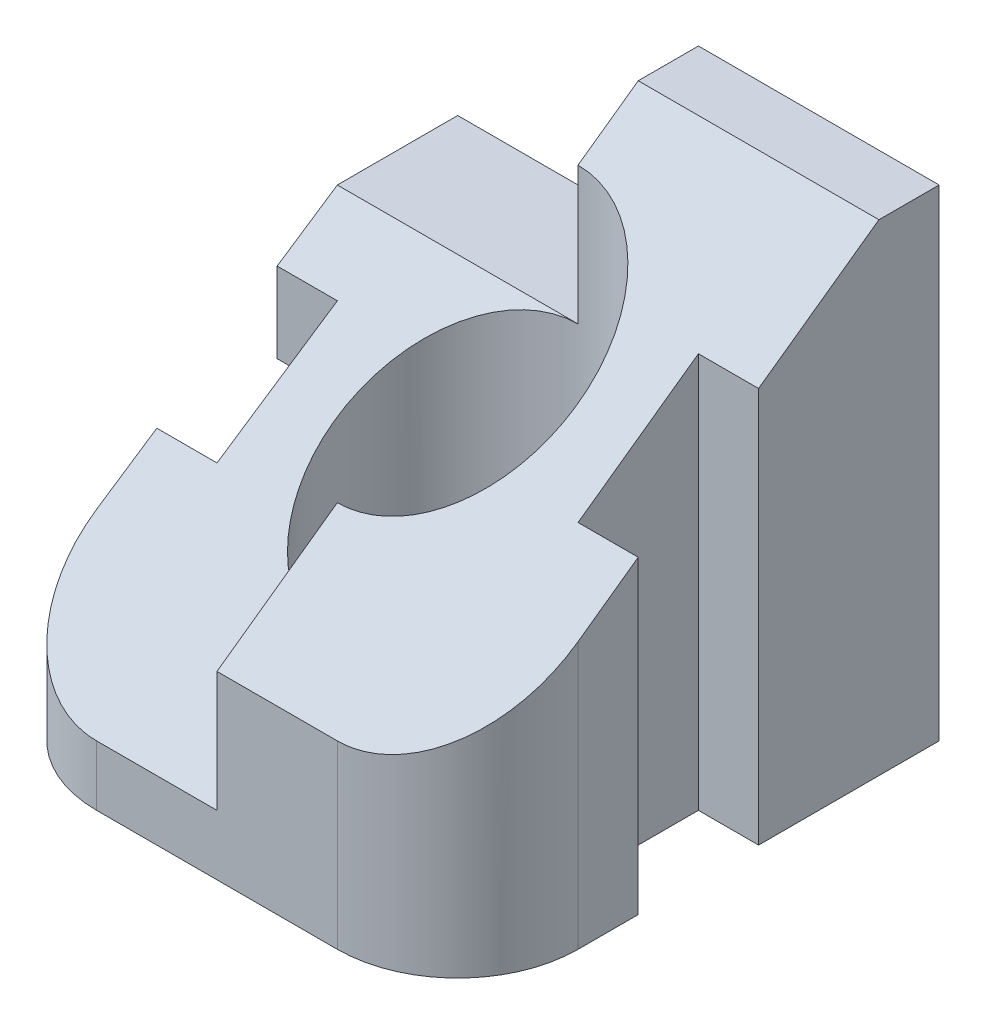
SolidWorks part; units mm, degrees
ref_plane "Front Plane" through (0, 0, 0) normal (0, 0, 1) x (1, 0, 0)
ref_plane "Top Plane" through (0, 0, 0) normal (0, 1, 0) x (1, 0, 0)
ref_plane "Right Plane" through (0, 0, 0) normal (1, 0, 0) x (0, 0, -1)
sketch "Sketch1" plane through (0, 0, 0) normal (0, 0, 1) x (1, 0, 0)
  line L1 (-20, 20) -> (20, 20)
  line L2 (-20, 20) -> (-20, -20)
  line L3 (-20, -20) -> (20, -20)
  line L4 (20, 20) -> (20, -20)
  line L5 (-20, 20) -> (20, -20) construction
  line L6 (-20, -20) -> (20, 20) construction
  point P0 (0, 0)
  dimension "D1" = 40
  dimension "D2" = 40
extrude "Boss-Extrude1" add sketch "Sketch1" along normal blind 40
sketch "Sketch2" plane through (0, 20, 0) normal (0, 1, 0) x (1, 0, 0)
  line L0 (20, 0) -> (-20, 0) construction
  line L1 (20, -40) -> (20, 0) construction
  circle A0 centre (0, -20) radius 10
  dimension "D1" = 20
  dimension "D2" = 20
  dimension "D3" = 20
extrude "Cut-Extrude1" cut sketch "Sketch2" against normal through all
sketch "Sketch3" plane through (0, 20, 0) normal (0, 1, 0) x (1, 0, 0)
  line L0 (20, -15) -> (15, -15)
  line L1 (20, -40) -> (20, 0) construction
  line L2 (15, -15) -> (15, -25)
  line L3 (15, -25) -> (20, -25)
  line L4 (20, -25) -> (20, -15)
  line L5 (-20, -15) -> (-15, -15)
  line L6 (-20, -40) -> (-20, 0) construction
  line L7 (-15, -15) -> (-15, -25)
  line L8 (-15, -25) -> (-20, -25)
  line L9 (-20, -25) -> (-20, -15)
  line L10 (20, 0) -> (-20, 0) construction
  dimension "D1" = 5
  dimension "D2" = 10
  dimension "D3" = 15
  dimension "D4" = 5
  dimension "D5" = 10
  dimension "D6" = 15
extrude "Cut-Extrude2" cut sketch "Sketch3" against normal through all
sketch "Sketch5" plane through (0, 20, 0) normal (0, 1, 0) x (1, 0, 0)
  line L0 (20, -40) -> (-20, -40) construction
  line L1 (-10, -40) -> (-20, -40)
  line L2 (-20, -40) -> (-20, -25) construction
  line L3 (-20, -40) -> (-20, -30)
  arc A0 (-10, -40) -> (-20, -30) centre (-10, -30) cw
  dimension "D1" = 10
  dimension "D2" = 10
extrude "Cut-Extrude5" cut sketch "Sketch5" against normal through all
sketch "Sketch7" plane through (0, 20, 0) normal (0, 1, 0) x (1, 0, 0)
  line L0 (20, -40) -> (-10, -40) construction
  line L1 (20, -40) -> (20, -25) construction
  line L2 (20, -30) -> (20, -40)
  line L3 (20, -40) -> (10, -40)
  arc A0 (10, -40) -> (20, -30) centre (10, -30) ccw
  dimension "D1" = 10
extrude "Cut-Extrude6" cut sketch "Sketch7" against normal through all
sketch "Sketch8" plane through (-20, 0, 0) normal (-1, 0, 0) x (0, 0, 1)
  line L0 (15, -20) -> (0, -20)
  line L1 (0, -20) -> (0, -5)
  line L2 (0, 20) -> (0, -20) construction
  line L3 (0, -5) -> (15, -5)
  line L4 (15, -20) -> (15, 20) construction
  line L5 (15, -5) -> (15, -20)
  dimension "D1" = 15
extrude "Cut-Extrude7" cut sketch "Sketch8" against normal blind 5
sketch "Sketch9" plane through (-20, 0, 0) normal (-1, 0, 0) x (0, 0, 1)
  line L0 (0, 20) -> (15, 20)
  line L1 (15, 20) -> (15, 5)
  line L2 (15, -5) -> (15, 20) construction
  line L3 (15, 5) -> (0, 5)
  line L4 (0, 20) -> (0, -5) construction
  line L5 (0, 5) -> (0, 20)
  dimension "D1" = 15
extrude "Cut-Extrude8" cut sketch "Sketch9" against normal blind 20
ref_plane "Plane1" through (-20, 0, 0) normal (1, 0, 0) x (0, 0, -1)
sketch "Sketch10" plane through (-20, 0, 0) normal (1, 0, 0) x (0, 0, -1)
  line L0 (-10, 5) -> (-40, -15)
  line L1 (-40, -20) -> (-40, 20) construction
  line L2 (-40, -15) -> (-40, 20)
  line L3 (-40, 20) -> (-10, 20)
  line L4 (-10, 20) -> (-10, 5)
  dimension "D1" = 5
extrude "Cut-Extrude9" cut sketch "Sketch10" along normal blind 20
ref_plane "Plane2" through (20, 0, 0) normal (1, 0, 0) x (0, 0, -1)
sketch "Sketch11" plane through (20, 0, 0) normal (1, 0, 0) x (0, 0, -1)
  line L0 (-5, 20) -> (-40, -5)
  line L1 (-15, 20) -> (0, 20) construction
  line L2 (-40, -20) -> (-40, 20) construction
  line L3 (-40, -5) -> (-40, 20)
  line L4 (-40, 20) -> (-5, 20)
  dimension "D1" = 5
  dimension "D2" = 15
extrude "Cut-Extrude10" cut sketch "Sketch11" against normal blind 20
